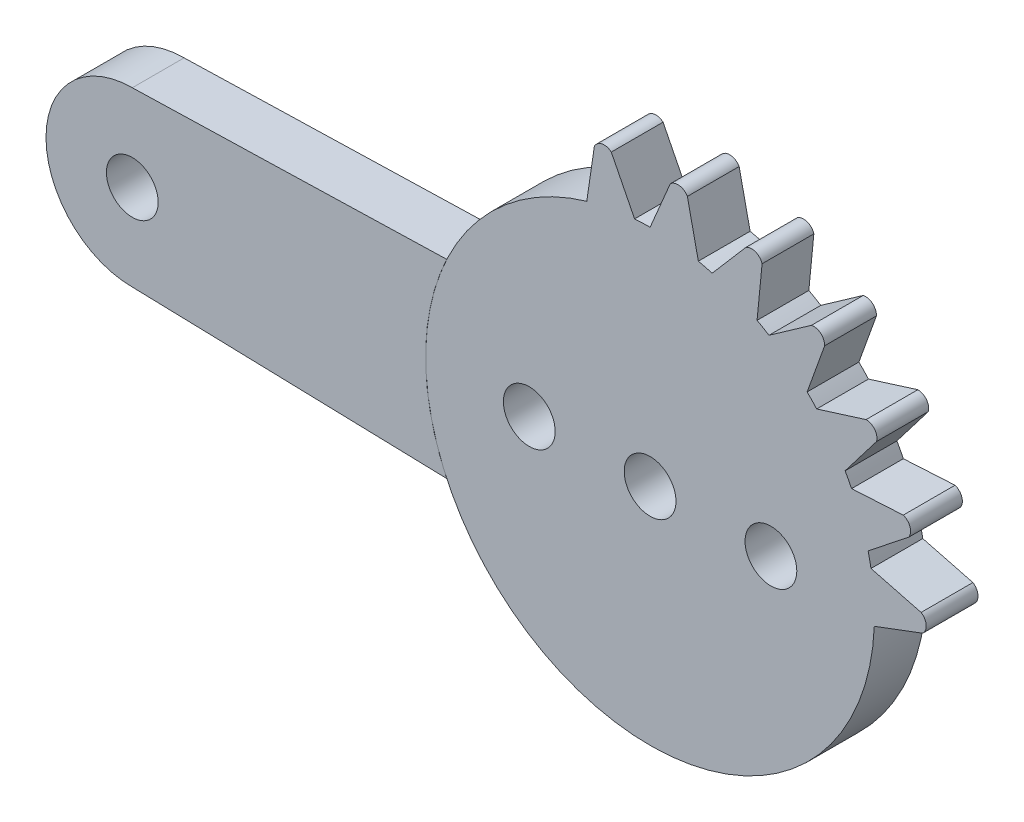
SolidWorks part; units mm, degrees
ref_plane "Piano frontale" through (0, 0, 0) normal (0, 0, 1) x (1, 0, 0)
ref_plane "Piano superiore" through (0, 0, 0) normal (0, 1, 0) x (1, 0, 0)
ref_plane "Piano destro" through (0, 0, 0) normal (1, 0, 0) x (0, 0, -1)
sketch "Schizzo1" plane through (0, 0, 0) normal (0, 0, 1) x (1, 0, 0)
  line L0 (-13, 0) -> (13, 0) construction
  circle A0 centre (0, 0) radius 13
  circle A1 centre (-7, 0) radius 1.5
  circle A2 centre (7, 0) radius 1.5
  circle A3 centre (0, 0) radius 1.5
  dimension "D1" = 26
  dimension "D4" = 3
  dimension "D5" = 3
  dimension "D6" = 3
  dimension "D2" = 7
  dimension "D3" = 7
sketch "Schizzo2" plane through (0, 0, 0) normal (0, 0, 1) x (1, 0, 0)
  line L0 (-7, 0) -> (-30, 0) construction
  line L1 (-30, 5) -> (-30, -5) construction
  line L6 (-30, 5) -> (-11.7792, 5.5)
  line L7 (-30, -5) -> (-11.7792, -5.5)
  circle A0 centre (-30, 0) radius 1.5
  arc A1 (-30, 5) -> (-30, -5) centre (-30, 0) ccw
  circle A2 centre (0, 0) radius 13 construction
  circle A3 centre (0, 0) radius 13.0045
  point P5 (-30, 5)
  point P8 (-30, -5)
  dimension "D2" = 3
  dimension "D4" = 10
  dimension "D3" = 11
  dimension "D5" = 26.009
  dimension "D1" = 23
sketch "Schizzo3" plane through (0, 0, 0) normal (0, 0, 1) x (1, 0, 0)
  line L0 (0, 13) -> (0, 0) construction
  line L1 (0, 0) -> (13, 0) construction
  line L2 (1.3976, 12.848) -> (0.8347, 12.9092) construction
  line L3 (0, -55) -> (0, 55) construction
  line L4 (1.3976, 12.848) -> (1.8006, 12.8041) construction
  line L5 (0, 13) -> (2.7952, 12.6959) construction
  line L6 (2.7952, 12.6959) -> (1.3976, 12.848) construction
  line L7 (0, 13) -> (-0.8685, 12.971) construction
  line L8 (-0.4495, 12.985) -> (-0.5424, 15.7635) construction
  line L9 (1.1676, 15.7635) -> (0, 13)
  line L10 (2.1601, 15.6279) -> (2.7952, 12.6959)
  line L11 (-3.2297, 15.4477) -> (-3.6676, 12.4798)
  line L12 (-2.2485, 15.6492) -> (-0.8989, 12.9699)
  line L13 (2.7952, 12.6959) -> (3.5952, 12.493) construction
  line L14 (3.1641, 12.6023) -> (3.1952, 12.5945) construction
  line L15 (3.1952, 12.5945) -> (3.5748, 14.0909) construction
  line L16 (5.5513, 14.7676) -> (3.5952, 12.493)
  line L17 (6.4883, 14.4136) -> (6.1973, 11.4277)
  line L18 (6.1973, 11.4277) -> (6.8885, 11.0249) construction
  line L19 (6.5429, 11.2263) -> (7.3923, 12.6837) construction
  line L20 (9.343, 12.7498) -> (6.8885, 11.0249)
  line L21 (10.1129, 12.109) -> (9.0979, 9.2859)
  line L22 (9.0979, 9.2859) -> (9.6518, 8.7087) construction
  line L23 (9.3749, 8.9973) -> (10.5474, 10.1226) construction
  line L24 (13.1229, 8.8113) -> (11.2986, 6.4297)
  line L25 (12.5142, 9.6069) -> (9.6518, 8.7087)
  line L26 (11.2986, 6.4297) -> (11.6727, 5.7226) construction
  line L27 (11.4857, 6.0762) -> (12.5229, 6.6249) construction
  line L28 (14.668, 5.8907) -> (11.6727, 5.7226)
  line L29 (14.9832, 4.9399) -> (12.6301, 3.0789)
  line L30 (12.6301, 3.0789) -> (12.7987, 2.2789) construction
  line L31 (12.7144, 2.6789) -> (14.1522, 2.9819) construction
  line L32 (15.7026, 1.5256) -> (12.7987, 2.2789)
  line L33 (15.7978, 0.5285) -> (12.9893, -0.5263)
  line L34 (-3.6676, 12.4798) -> (-0.8989, 12.9699) construction
  line L35 (-3.6676, 12.4798) -> (-0.8989, 12.9699)
  circle A0 centre (0, 0) radius 13 construction
  arc A1 (1.1676, 15.7635) -> (2.1601, 15.6279) centre (1.6117, 15.314) cw
  arc A2 (-2.2485, 15.6492) -> (-3.2297, 15.4477) centre (-2.6616, 15.1711) ccw
  arc A3 (6.4883, 14.4136) -> (5.5513, 14.7676) centre (5.8837, 14.2303) ccw
  arc A4 (9.343, 12.7498) -> (10.1129, 12.109) centre (9.4815, 12.1334) cw
  arc A5 (13.1229, 8.8113) -> (12.5142, 9.6069) centre (12.5126, 8.975) ccw
  arc A6 (14.668, 5.8907) -> (14.9832, 4.9399) centre (14.46, 5.2941) cw
  arc A7 (15.7978, 0.5285) -> (15.7026, 1.5256) centre (15.3667, 0.9904) ccw
  circle A8 centre (0, 0) radius 13
  point P13 (2.7952, 12.6959)
  dimension "D8" = 0.8685
  dimension "D18" = 3
  dimension "D20" = 26
  dimension "D15" = 0.6318
  dimension "D1" = 2.4753
  dimension "D2" = 1.0017
  dimension "D3" = 2.8732
  dimension "D4" = 3
  dimension "D5" = 3
  dimension "D6" = 2.8117
  dimension "D7" = 2.82
  dimension "D9" = 0.8
  dimension "D10" = 0.8
  dimension "D11" = 0.8253
  dimension "D12" = 0.8
  dimension "D13" = 0.8
  dimension "D14" = 0.8
  dimension "D16" = 3
  dimension "D17" = 2.7229
  dimension "D19" = 2.8418
extrude "Estrusione-Estrusione1" add sketch "Schizzo1" along normal blind 3
extrude "Estrusione-Estrusione2" add sketch "Schizzo2" along normal blind 3 contours A3 L6 A1 L7 A0
extrude "Estrusione-Estrusione3" add sketch "Schizzo3" along normal blind 3 contours A8 L35 L12 A2 L11 | A8 L10 A1 L9 | A8 L17 A3 L16 | A8 L21 A4 L20 | A8 L24 A5 L25 | A8 L29 A6 L28 | A8 L33 A7 L32
